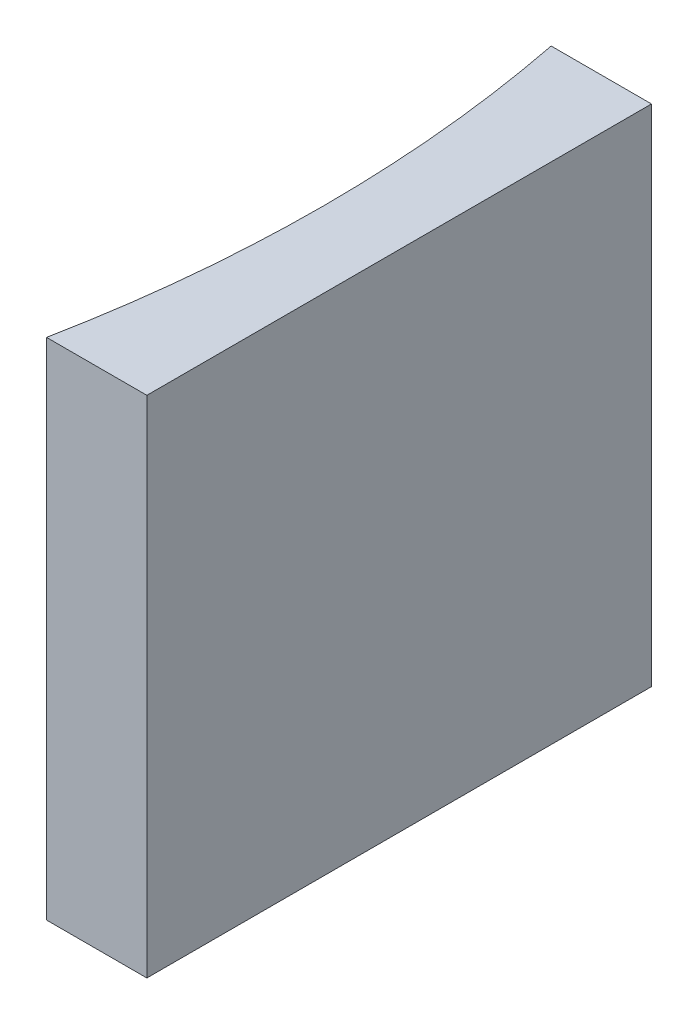
SolidWorks part; units mm, degrees
ref_plane "前视基准面" through (0, 0, 0) normal (0, 0, 1) x (1, 0, 0)
ref_plane "上视基准面" through (0, 0, 0) normal (0, 1, 0) x (1, 0, 0)
ref_plane "右视基准面" through (0, 0, 0) normal (1, 0, 0) x (0, 0, -1)
sketch "草图1" plane through (0, 0, 0) normal (0, 1, 0) x (1, 0, 0)
  line L0 (0, 0) -> (0, -20)
  line L1 (0, 0) -> (-3.9775, 0)
  line L2 (0, -20) -> (-3.9775, -20)
  line L3 (8.2336, -10) -> (-10.4405, -10) construction
  arc A0 (-3.9775, -20) -> (-3.9775, 0) centre (-54.64, -10) ccw
  point P7 (-3, -10)
  point P8 (0, -10)
  dimension "D2" = 51.64
  dimension "D3" = 3
  dimension "D1" = 20
extrude "凸台-拉伸1" add sketch "草图1" along normal blind 20
